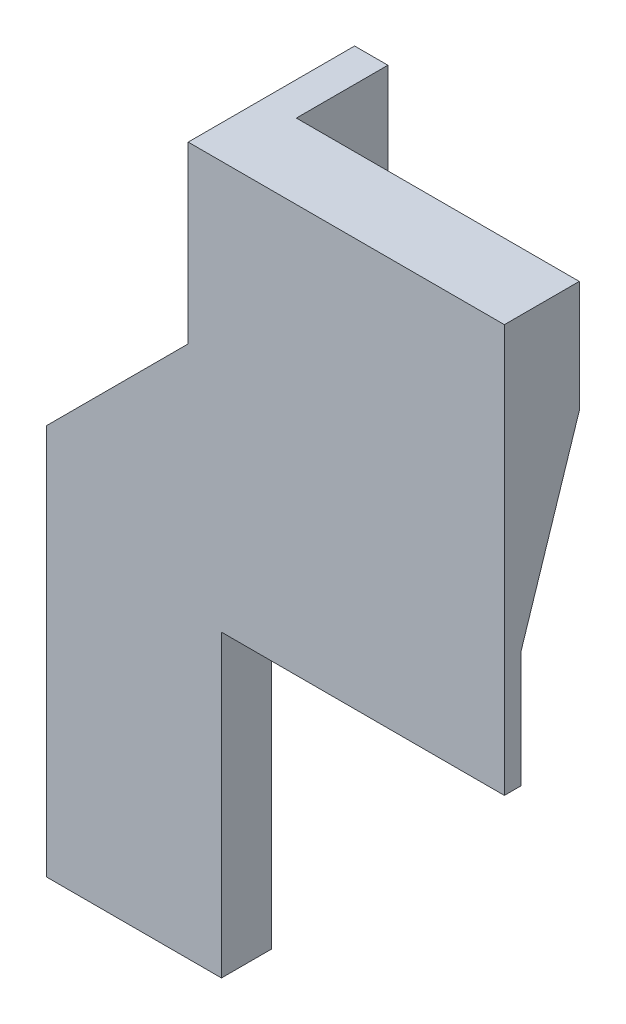
SolidWorks part; units mm, degrees
material "PLA"
ref_plane "Front Plane" through (0, 0, 0) normal (0, 0, 1) x (1, 0, 0)
ref_plane "Top Plane" through (0, 0, 0) normal (0, 1, 0) x (1, 0, 0)
ref_plane "Right Plane" through (0, 0, 0) normal (1, 0, 0) x (0, 0, -1)
sketch "Sketch1" plane through (0, 0, 0) normal (0, 0, 1) x (1, 0, 0)
  line L0 (-15, 0) -> (-15, 36)
  line L1 (-15, 36) -> (15, 36)
  line L2 (-15, 50) -> (-15, 111)
  line L3 (-15, 111) -> (15, 111)
  line L4 (15, 50) -> (15, 111)
  line L5 (-30, 0) -> (0, 0) construction
  line L6 (-30, 0) -> (-30, 50)
  line L7 (-30, 50) -> (-15, 50)
  line L8 (15, 50) -> (15, 36)
  line L9 (-30, 0) -> (-15, 0)
  point P3 (0, 111)
  dimension "D1" = 75
  dimension "D2" = 15
  dimension "D3" = 50
  dimension "D4" = 30
  dimension "D5" = 14
extrude "Boss-Extrude1" add sketch "Sketch1" along normal blind 2
sketch "Sketch2" plane through (15, 0, 0) normal (1, 0, 0) x (0, 0, -1)
  line L1 (0, 50) -> (7, 71.5438)
  line L3 (7, 71.5438) -> (7, 111)
  line L4 (0, 36) -> (0, 111) construction
  line L5 (0, 50) -> (0, 111)
  line L6 (7, 111) -> (0, 111)
  dimension "D1" = 7
  dimension "D2" = 18
  dimension "D3" = 14
extrude "Boss-Extrude2" add sketch "Sketch2" against normal up to surface (30 mm away) up to face at (-15, 80.5, 1)
sketch "Sketch3" plane through (0, 0, 0) normal (0, 0, -1) x (-1, 0, 0)
  line L0 (15, 50) -> (30, 50) construction
  line L1 (30, 0) -> (15, 0) construction
  line L2 (15, 0) -> (15, 36) construction
  line L3 (30, 50) -> (30, 0) construction
  line L4 (15, 50) -> (30, 50)
  line L5 (30, 0) -> (15, 0)
  line L6 (15, 0) -> (15, 50)
  line L7 (30, 50) -> (30, 0)
  point P4 (15, 48.9938)
extrude "Boss-Extrude3" add sketch "Sketch3" along normal blind 4
sketch "Sketch4" plane through (0, 0, -4) normal (0, 0, -1) x (-1, 0, 0)
  line L0 (15, 111) -> (15, 50) construction
  line L1 (15, 111) -> (15, 50)
  line L2 (30, 50) -> (15, 50) construction
  line L3 (30, 50) -> (15, 50)
  line L4 (30, 0) -> (30, 50)
  line L5 (19, 111) -> (15, 111)
  line L6 (30, 0) -> (36, 0)
  line L7 (30, 0) -> (30, 50) construction
  line L8 (36, 0) -> (36, 47)
  line L9 (36, 47) -> (19, 64)
  line L10 (19, 64) -> (19, 111)
  line L11 (30, 0) -> (15, 0) construction
  point P3 (33, 0)
  dimension "D1" = 4
  dimension "D2" = 45
  dimension "D3" = 17
  dimension "D4" = 47
extrude "Boss-Extrude4" add sketch "Sketch4" against normal up to surface (6 mm away) up to face at (-11.25, 49.25, 2)
sketch "Sketch5" plane through (0, 0, -4) normal (0, 0, -1) x (-1, 0, 0)
  line L0 (32, 0) -> (32, 45.3431)
  line L1 (32, 45.3431) -> (15, 62.3431)
  line L2 (32, 45.3431) -> (16.1716, 61.1716) construction
  line L3 (15, 111) -> (15, 62.3107) construction
  line L7 (15, 111) -> (15, 62.3107)
  line L8 (15, 62.3107) -> (15, 0)
  line L9 (15, 0) -> (36, 0)
  line L10 (36, 0) -> (36, 47)
  line L11 (36, 47) -> (19, 64)
  line L12 (19, 64) -> (19, 111)
  line L13 (19, 111) -> (15, 111)
  line L14 (15, 111) -> (15, 62.3431)
  line L16 (32, 0) -> (36, 0)
  line L17 (36, 0) -> (36, 47)
  line L18 (36, 47) -> (19, 64)
  line L19 (19, 64) -> (19, 111)
  line L20 (19, 111) -> (15, 111)
  point P10 (15, 68.9783)
  dimension "D1" = 0
  dimension "D2" = 4
extrude "Boss-Extrude5" add sketch "Sketch5" along normal blind 14
sketch "Sketch6" plane through (0, 111, 0) normal (0, 1, 0) x (1, 0, 0)
  line L6 (15, 7) -> (-15, 7)
  line L7 (-15, 7) -> (-15, 18)
  line L8 (-15, 18) -> (-19, 18)
  line L9 (-19, 18) -> (-19, -2)
  line L10 (-19, -2) -> (15, -2)
  line L11 (15, -2) -> (15, 7)
  line L12 (15, 7) -> (-15, 7)
  line L13 (-15, 7) -> (-15, 18)
  line L14 (-15, 18) -> (-19, 18)
  line L15 (-19, 18) -> (-19, -2)
  line L16 (-19, -2) -> (15, -2)
  line L17 (15, -2) -> (15, 7)
  dimension "D1" = 0
extrude "Cut-Extrude1" cut sketch "Sketch6" against normal blind 26
sketch "Sketch7" plane through (15, 0, 0) normal (1, 0, 0) x (0, 0, -1)
  line L6 (7, 85) -> (-2, 85)
  line L7 (-2, 85) -> (-2, 36)
  line L8 (-2, 36) -> (0, 36)
  line L9 (0, 36) -> (0, 50)
  line L10 (0, 50) -> (7, 71.5438)
  line L11 (7, 71.5438) -> (7, 85)
  line L12 (7, 85) -> (-2, 85)
  line L13 (-2, 85) -> (-2, 36)
  line L14 (-2, 36) -> (0, 36)
  line L15 (0, 36) -> (0, 50)
  line L16 (0, 50) -> (7, 71.5438)
  line L17 (7, 71.5438) -> (7, 85)
  dimension "D1" = 0
extrude "Boss-Extrude6" add sketch "Sketch7" along normal blind 4
